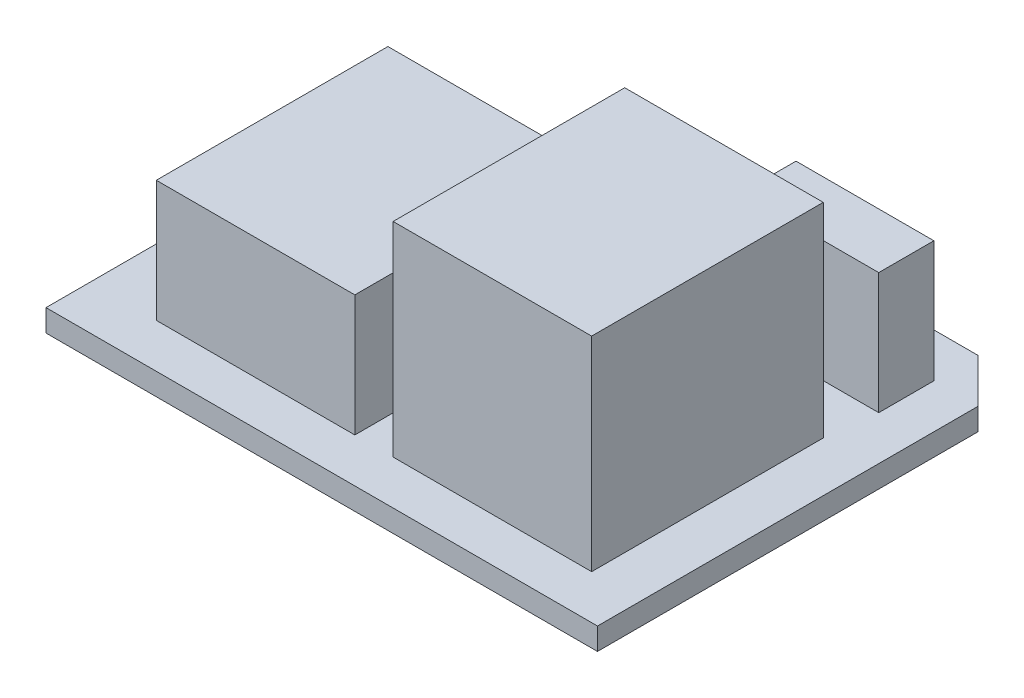
SolidWorks part; units mm, degrees
ref_plane "Płaszczyzna przednia" through (0, 0, 0) normal (0, 0, 1) x (1, 0, 0)
ref_plane "Płaszczyzna górna" through (0, 0, 0) normal (0, 1, 0) x (1, 0, 0)
ref_plane "Płaszczyzna prawa" through (0, 0, 0) normal (1, 0, 0) x (0, 0, -1)
sketch "Sketch1" plane through (0, 0, 0) normal (0, 1, 0) x (1, 0, 0)
  line L0 (-25, 12.75) -> (-1, 12.75)
  line L1 (-25, 19.25) -> (25, 19.25)
  line L2 (-25, 19.25) -> (-25, -19.25)
  line L3 (-25, -19.25) -> (25, -19.25)
  line L4 (25, 19.25) -> (25, -19.25)
  line L5 (-25, 19.25) -> (25, -19.25) construction
  line L6 (-25, -19.25) -> (25, 19.25) construction
  line L7 (-20, 12.75) -> (-25, 7.75)
  line L8 (-1, 12.75) -> (5.5, 19.25)
  line L9 (21, 19.25) -> (25, 15.25)
  point P0 (0, 0)
  dimension "D1" = 38.5
  dimension "D2" = 50
  dimension "D3" = 32
  dimension "D4" = 24
  dimension "D5" = 5
  dimension "D6" = 5
  dimension "D7" = 6.5
  dimension "D8" = 4
  dimension "D9" = 4
extrude "Boss-Extrude1" add sketch "Sketch1" along normal blind 2 contours L9 L1 L8 L0 L7 L2 L3 L4
sketch "Sketch2" plane through (0, 2, 0) normal (0, 1, 0) x (1, 0, 0)
  line L0 (-25, 7.75) -> (-25, -19.25) construction
  line L1 (-19, 5.75) -> (-1, 5.75)
  line L2 (-19, 5.75) -> (-19, -15.25)
  line L3 (-19, -15.25) -> (-1, -15.25)
  line L4 (-1, 5.75) -> (-1, -15.25)
  line L5 (-19, 5.75) -> (-1, -15.25) construction
  line L6 (-19, -15.25) -> (-1, 5.75) construction
  line L7 (-25, -19.25) -> (25, -19.25) construction
  point P0 (-10, -4.75)
  dimension "D1" = 21
  dimension "D2" = 18
  dimension "D3" = 6
  dimension "D4" = 4
extrude "Boss-Extrude2" add sketch "Sketch2" along normal blind 11
sketch "Sketch3" plane through (0, 2, 0) normal (0, 1, 0) x (1, 0, 0)
  line L0 (-25, -19.25) -> (25, -19.25) construction
  line L1 (2.4711, 5.75) -> (20.4711, 5.75)
  line L2 (2.4711, 5.75) -> (2.4711, -15.25)
  line L3 (2.4711, -15.25) -> (20.4711, -15.25)
  line L4 (20.4711, 5.75) -> (20.4711, -15.25)
  line L5 (2.4711, 5.75) -> (20.4711, -15.25) construction
  line L6 (2.4711, -15.25) -> (20.4711, 5.75) construction
  point P0 (11.4711, -4.75)
  dimension "D1" = 18
  dimension "D2" = 21
  dimension "D3" = 4
extrude "Boss-Extrude3" add sketch "Sketch3" along normal blind 18.5
sketch "Sketch4" plane through (0, 2, 0) normal (0, 1, 0) x (1, 0, 0)
  line L0 (25, 15.25) -> (25, -19.25) construction
  line L1 (8.5, 15.25) -> (21, 15.25)
  line L2 (8.5, 15.25) -> (8.5, 10.25)
  line L3 (8.5, 10.25) -> (21, 10.25)
  line L4 (21, 15.25) -> (21, 10.25)
  line L5 (8.5, 15.25) -> (21, 10.25) construction
  line L6 (8.5, 10.25) -> (21, 15.25) construction
  line L7 (5.5, 19.25) -> (21, 19.25) construction
  point P0 (14.75, 12.75)
  dimension "D1" = 12.5
  dimension "D2" = 5
  dimension "D3" = 4
  dimension "D4" = 4
extrude "Boss-Extrude4" add sketch "Sketch4" along normal blind 11
